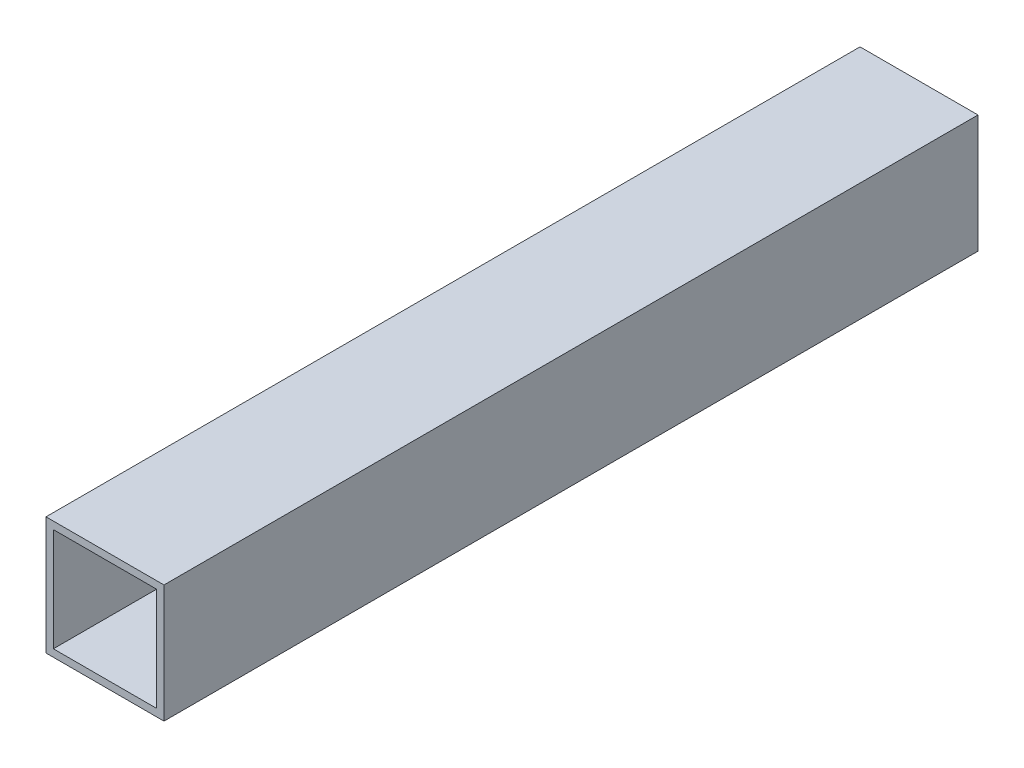
SolidWorks part; units mm, degrees
material "ALUMINUM 6061-T6"
ref_plane "Front Plane" through (0, 0, 0) normal (0, 0, 1) x (1, 0, 0)
ref_plane "Top Plane" through (0, 0, 0) normal (0, 1, 0) x (1, 0, 0)
ref_plane "Right Plane" through (0, 0, 0) normal (1, 0, 0) x (0, 0, -1)
sketch "Sketch1" plane through (0, 0, 0) normal (0, 0, 1) x (1, 0, 0)
  line L1 (-12.7, -12.7) -> (12.7, -12.7)
  line L2 (-12.7, -12.7) -> (-12.7, 12.7)
  line L3 (-12.7, 12.7) -> (12.7, 12.7)
  line L4 (12.7, -12.7) -> (12.7, 12.7)
  line L5 (-12.7, -12.7) -> (12.7, 12.7) construction
  line L6 (-12.7, 12.7) -> (12.7, -12.7) construction
  point P0 (0, 0)
  dimension "D1" = 25.4
  dimension "D2" = 25.4
extrude "Boss-Extrude1" add sketch "Sketch1" along normal mid plane 175.26
sketch "Sketch2" plane through (0, 0, 87.63) normal (0, 0, 1) x (1, 0, 0)
  line L0 (12.7, 12.7) -> (-12.7, 12.7) construction
  line L1 (-11.1125, -11.1125) -> (11.1125, -11.1125)
  line L2 (-11.1125, -11.1125) -> (-11.1125, 11.1125)
  line L3 (-11.1125, 11.1125) -> (11.1125, 11.1125)
  line L4 (11.1125, -11.1125) -> (11.1125, 11.1125)
  line L5 (-11.1125, -11.1125) -> (11.1125, 11.1125) construction
  line L6 (-11.1125, 11.1125) -> (11.1125, -11.1125) construction
  line L7 (-12.7, 12.7) -> (-12.7, -12.7) construction
  point P0 (0, 0)
  dimension "D1" = 1.5875
  dimension "D2" = 1.5875
extrude "Cut-Extrude1" cut sketch "Sketch2" against normal through all
